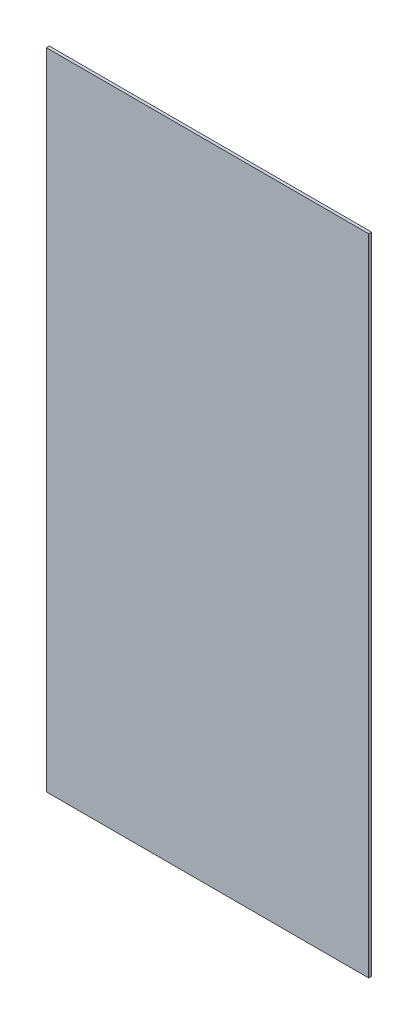
SolidWorks part; units mm, degrees
material "OSB_Plywood"
ref_plane "Front Plane" through (0, 0, 0) normal (0, 0, 1) x (1, 0, 0)
ref_plane "Top Plane" through (0, 0, 0) normal (0, 1, 0) x (1, 0, 0)
ref_plane "Right Plane" through (0, 0, 0) normal (1, 0, 0) x (0, 0, -1)
sketch "Sketch1" plane through (0, 0, 0) normal (0, 0, 1) x (1, 0, 0)
  line L1 (0, 0) -> (1219.2, 0)
  line L2 (0, 0) -> (0, 2438.4)
  line L3 (0, 2438.4) -> (1219.2, 2438.4)
  line L4 (1219.2, 0) -> (1219.2, 2438.4)
  dimension "D1" = 1219.2
  dimension "D2" = 2438.4
extrude "Boss-Extrude1" add sketch "Sketch1" along normal blind 11.1125
